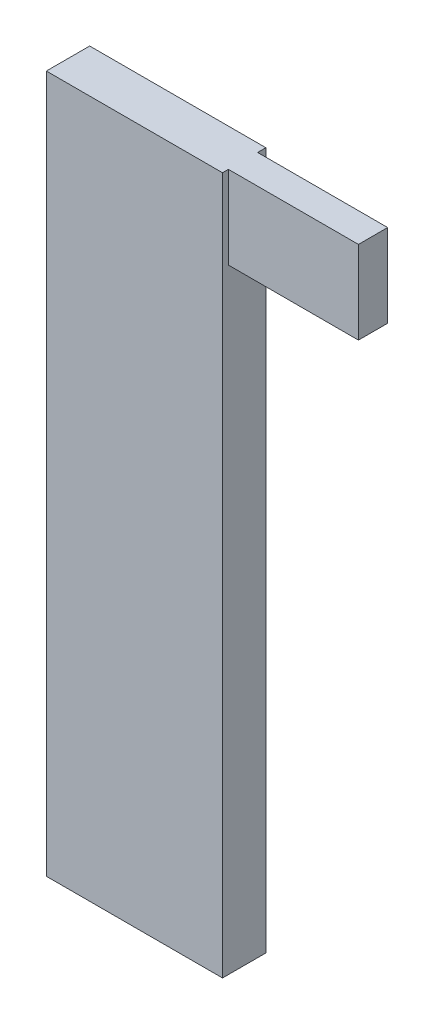
SolidWorks part; units mm, degrees
ref_plane "Front Plane" through (0, 0, 0) normal (0, 0, 1) x (1, 0, 0)
ref_plane "Top Plane" through (0, 0, 0) normal (0, 1, 0) x (1, 0, 0)
ref_plane "Right Plane" through (0, 0, 0) normal (1, 0, 0) x (0, 0, -1)
sketch "Sketch1" plane through (0, 0, 0) normal (0, 0, 1) x (1, 0, 0)
  line L0 (-37.5648, 18.053) -> (-32.4024, 18.053)
  line L3 (-37.5648, -2.382) -> (-37.5648, 18.053)
  line L6 (-37.5648, 18.053) -> (-32.4024, 18.053)
  line L7 (-37.5648, 18.053) -> (-37.5648, -2.382)
  line L8 (-37.5648, -2.382) -> (-32.4024, -2.382)
  line L9 (-32.4024, 18.053) -> (-32.4024, -2.382)
  line L12 (-32.4024, 16.6244) -> (-32.4024, -2.382)
  line L15 (-32.4024, -2.382) -> (-37.5648, -2.382)
extrude "Boss-Extrude1" add sketch "Sketch1" along normal blind 1.27 contours L7 L6 L9 L8
sketch "Sketch2" plane through (-37.5648, 0, 0) normal (-1, 0, 0) x (0, 0, 1)
  line L10 (0.1917, 16.874) -> (1.0307, 16.874)
  line L11 (0.1917, 16.874) -> (0.1917, 12.9918)
  line L12 (0.1917, 12.9918) -> (1.0307, 12.9918)
  line L13 (1.0307, 16.874) -> (1.0307, 12.9918)
extrude "Cut-Extrude1" cut sketch "Sketch2" against normal blind 3.81
sketch "Sketch3" plane through (-32.4024, 0, 0) normal (1, 0, 0) x (0, 0, -1)
  line L0 (-1.0972, 18.053) -> (-1.0972, 15.6235)
  line L1 (-1.27, 18.053) -> (0, 18.053) construction
  line L2 (-1.0972, 15.6235) -> (-0.2409, 15.6235)
  line L3 (-0.2409, 15.6235) -> (-0.2409, 18.053)
  line L4 (-0.2409, 18.053) -> (-1.0972, 18.053)
extrude "Boss-Extrude2" add sketch "Sketch3" along normal blind 3.81
